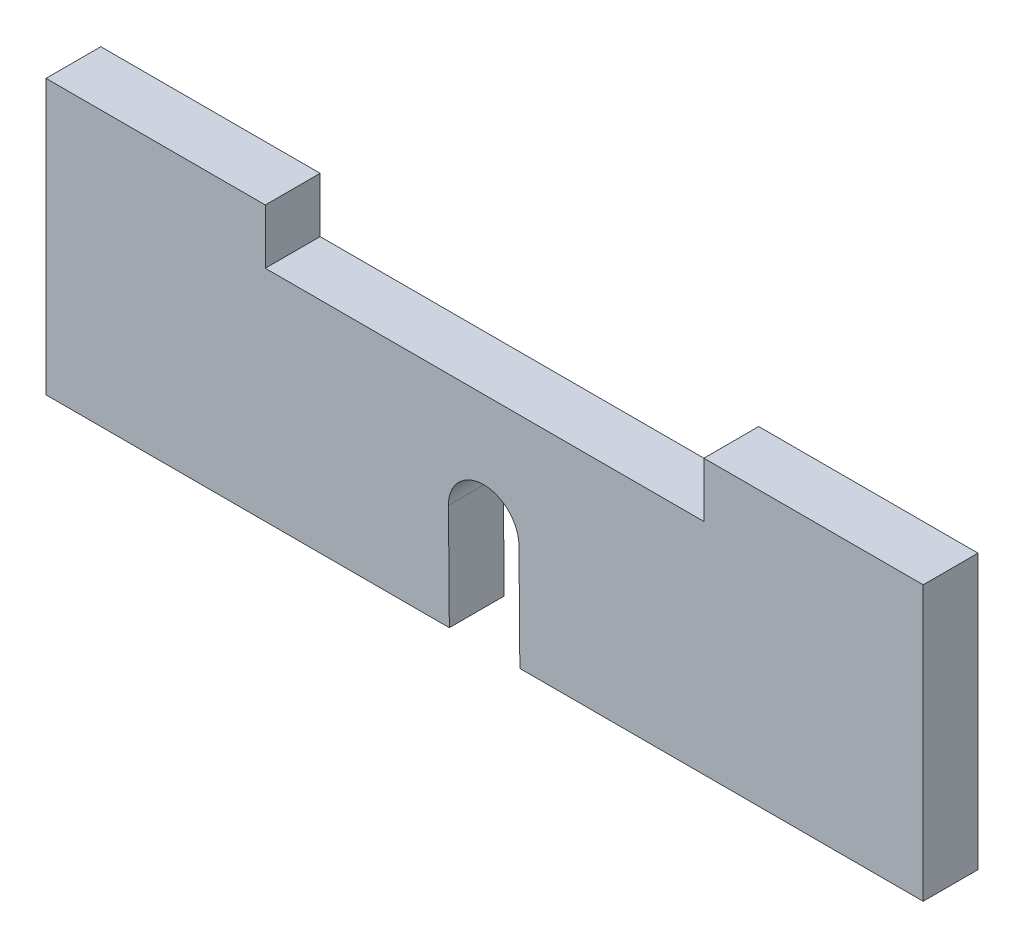
SolidWorks part; units mm, degrees
ref_plane "Front Plane" through (0, 0, 0) normal (0, 0, 1) x (1, 0, 0)
ref_plane "Top Plane" through (0, 0, 0) normal (0, 1, 0) x (1, 0, 0)
ref_plane "Right Plane" through (0, 0, 0) normal (1, 0, 0) x (0, 0, -1)
sketch "Sketch1" plane through (0, 0, 0) normal (0, 0, 1) x (1, 0, 0)
  line L1 (0, 0) -> (50.8, 0)
  line L2 (0, 0) -> (0, 12.7)
  line L3 (0, 12.7) -> (50.8, 12.7)
  line L4 (50.8, 0) -> (50.8, 12.7)
  dimension "D1" = 50.8
  dimension "D2" = 12.7
extrude "Extrude1" add sketch "Sketch1" along normal blind 3.175
sketch "Sketch3" plane through (0, 12.7, 0) normal (0, 1, 0) x (1, 0, 0)
  line L0 (50.8, -3.175) -> (0, -3.175) construction
  line L1 (0, 0) -> (12.7, 0)
  line L2 (0, 0) -> (0, -3.175)
  line L3 (0, -3.175) -> (12.7, -3.175)
  line L4 (12.7, 0) -> (12.7, -3.175)
  dimension "D1" = 3.175
  dimension "D2" = 12.7
extrude "Extrude3" add sketch "Sketch3" along normal blind 3.175
pattern_linear "LPattern1" count 2 spacing 38.1 along (1, 0, 0) of "Extrude3"
sketch "Sketch4" plane through (0, 0, 3.175) normal (0, 0, 1) x (1, 0, 0)
  line L0 (25.3497, 6.1282) -> (25.4, 0) construction
  line L1 (0, 0) -> (50.8, 0) construction
  line L2 (27.3917, 6.1449) -> (27.4419, 0.0167)
  line L3 (23.3078, 6.1114) -> (23.3581, -0.0167)
  arc A0 (27.3917, 6.1449) -> (23.3078, 6.1114) centre (25.3497, 6.1282) ccw
  arc A1 (23.3581, -0.0167) -> (27.4419, 0.0167) centre (25.4, 0) ccw
  point P4 (25.3749, 3.0641)
extrude "Extrude4" cut sketch "Sketch4" against normal through all
